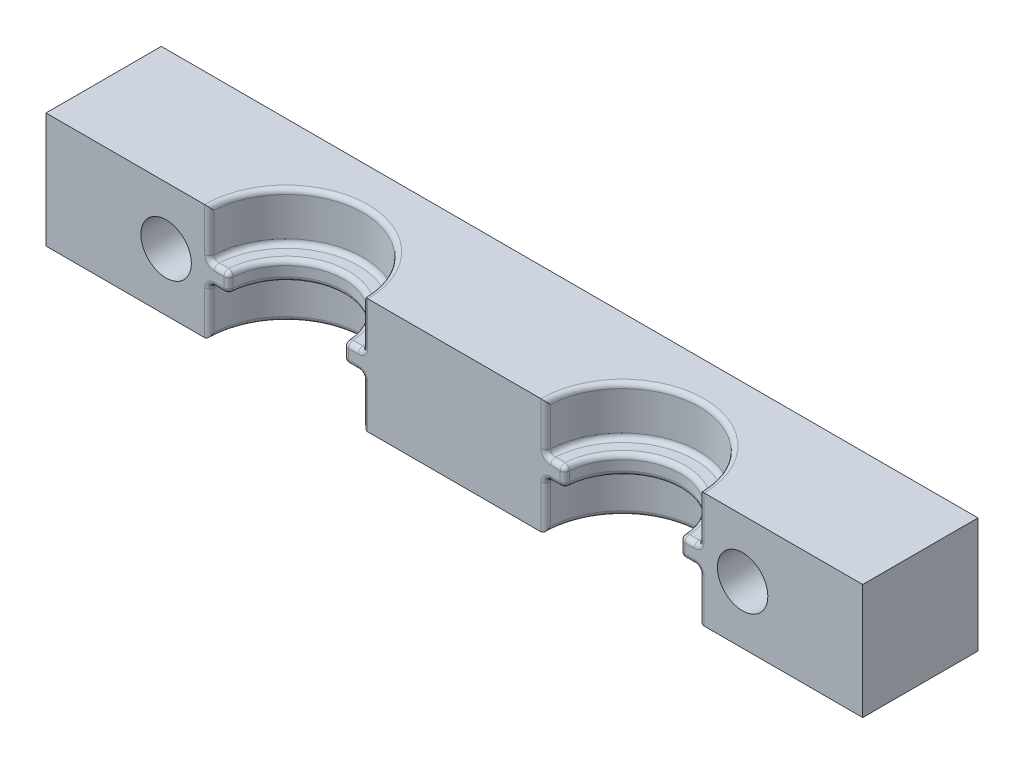
SolidWorks part; units mm, degrees
ref_plane "Front Plane" through (0, 0, 0) normal (0, 0, 1) x (1, 0, 0)
ref_plane "Top Plane" through (0, 0, 0) normal (0, 1, 0) x (1, 0, 0)
ref_plane "Right Plane" through (0, 0, 0) normal (1, 0, 0) x (0, 0, -1)
sketch "Sketch1" plane through (0, 0, 0) normal (0, 0, 1) x (1, 0, 0)
  line L1 (-42.5, -6) -> (42.5, -6)
  line L2 (-42.5, -6) -> (-42.5, 6)
  line L3 (-42.5, 6) -> (42.5, 6)
  line L4 (42.5, -6) -> (42.5, 6)
  line L5 (-42.5, -6) -> (42.5, 6) construction
  line L6 (-42.5, 6) -> (42.5, -6) construction
  point P0 (0, 0)
  dimension "D1" = 85
  dimension "D2" = 12
extrude "Boss-Extrude1" add sketch "Sketch1" along normal blind 12
sketch "Sketch2" plane through (0, 6, 0) normal (0, 1, 0) x (1, 0, 0)
  line L0 (42.5, -12) -> (-42.5, -12) construction
  line L1 (-42.5, -12) -> (-42.5, 0) construction
  line L2 (42.5, -12) -> (42.5, 0) construction
  circle A0 centre (-17.5, -12) radius 8
  circle A1 centre (17.5, -12) radius 8
  dimension "D1" = 16
  dimension "D2" = 16
  dimension "D3" = 25
  dimension "D4" = 25
extrude "Cut-Extrude2" cut sketch "Sketch2" against normal blind 5
sketch "Sketch3" plane through (0, -6, 0) normal (0, -1, 0) x (1, 0, 0)
  line L0 (-42.5, 12) -> (42.5, 12) construction
  line L1 (-42.5, 12) -> (-42.5, 0) construction
  line L2 (42.5, 12) -> (42.5, 0) construction
  circle A0 centre (-17.5, 12) radius 8
  circle A1 centre (17.5, 12) radius 8
  dimension "D1" = 16
  dimension "D2" = 16
  dimension "D3" = 25
  dimension "D4" = 25
extrude "Cut-Extrude3" cut sketch "Sketch3" against normal blind 5
sketch "Sketch4" plane through (0, 0, 0) normal (0, 1, 0) x (1, 0, 0)
  line L0 (-25.5, -12) -> (-9.5, -12) construction
  line L1 (9.5, -12) -> (25.5, -12) construction
  circle A0 centre (-17.5, -12) radius 6
  circle A1 centre (17.5, -12) radius 6
  dimension "D1" = 12
  dimension "D2" = 12
extrude "Cut-Extrude4" cut sketch "Sketch4" against normal through all both and the other way through all
sketch "Sketch5" plane through (0, 0, 12) normal (0, 0, 1) x (1, 0, 0)
  line L0 (-42.5, 0) -> (-30, 0) construction
  line L1 (-42.5, 6) -> (-42.5, -6) construction
  line L2 (42.5, 0) -> (30, 0) construction
  line L3 (42.5, -6) -> (42.5, 6) construction
  circle A0 centre (-30, 0) radius 2.625
  circle A1 centre (30, 0) radius 2.625
  dimension "D3" = 5.25
  dimension "D4" = 5.25
  dimension "D1" = 12.5
  dimension "D2" = 12.5
  dimension "D5" = 60
extrude "Cut-Extrude6" cut sketch "Sketch5" against normal through all
fillet "Fillet1" radius 0.5 32 edges at (-10.5, 1, 12) (-24.5, 1, 12) (-24.5, -1, 12) (-10.5, -1, 12) (10.5, -1, 12) (24.5, -1, 12) (24.5, 1, 12) (10.5, 1, 12) (-9.5, 3.5, 12) (-25.5, 3.5, 12) (-17.5, 6, 4) (-17.5, 1, 4) (-25.5, -3.5, 12) (-9.5, -3.5, 12) (-17.5, -6, 4) (-17.5, -1, 4) (9.5, -3.5, 12) (25.5, -3.5, 12) (17.5, -6, 4) (17.5, -1, 4) (25.5, 3.5, 12) (9.5, 3.5, 12) (17.5, 6, 4) (17.5, 1, 4) (11.5, 0, 12) (23.5, 0, 12) (17.5, -1, 6) (17.5, 1, 6) (-23.5, 0, 12) (-11.5, 0, 12) (-17.5, -1, 6) (-17.5, 1, 6)
